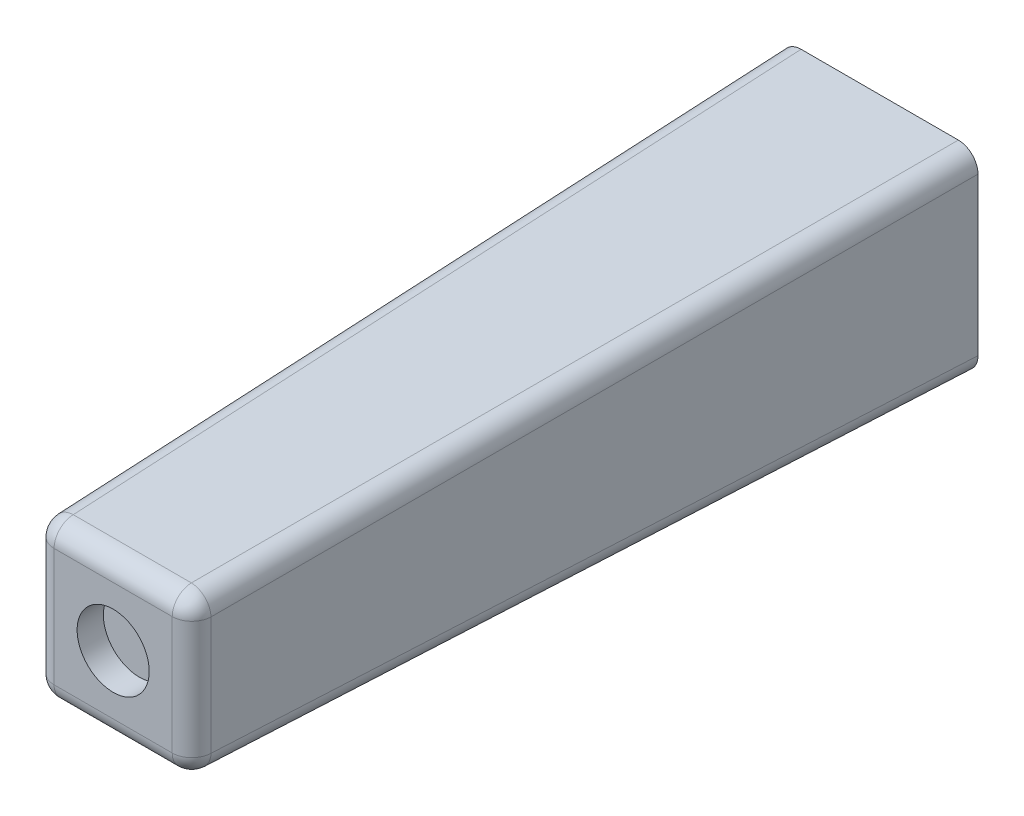
SolidWorks part; units mm, degrees
ref_plane "Спереди" through (0, 0, 0) normal (0, 0, 1) x (1, 0, 0)
ref_plane "Сверху" through (0, 0, 0) normal (0, 1, 0) x (1, 0, 0)
ref_plane "Справа" through (0, 0, 0) normal (1, 0, 0) x (0, 0, -1)
other "Configuration Table"
sketch "Sketch1" plane through (0, 0, 0) normal (0, 0, 1) x (1, 0, 0)
  line L1 (-7.5, -7.5) -> (7.5, -7.5)
  line L2 (-7.5, -7.5) -> (-7.5, 7.5)
  line L3 (-7.5, 7.5) -> (7.5, 7.5)
  line L4 (7.5, -7.5) -> (7.5, 7.5)
  line L5 (-7.5, -7.5) -> (7.5, 7.5) construction
  line L6 (-7.5, 7.5) -> (7.5, -7.5) construction
  point P0 (0, 0)
  dimension "D1" = 15
  dimension "D2" = 15
extrude "Boss-Extrude1" add sketch "Sketch1" along normal blind 58.5 draft 1.5
sketch "Sketch2" plane through (0, 0, 0) normal (0, 0, -1) x (-1, 0, 0)
  circle A0 centre (0, 0) radius 1.5
  dimension "D1" = 3
extrude "Cut-Extrude1" cut sketch "Sketch2" against normal blind 10
sketch "Sketch3" plane through (0, 0, 58.5) normal (0, 0, 1) x (1, 0, 0)
  circle A0 centre (0, 0) radius 2.75
  dimension "D1" = 5.5
extrude "Cut-Extrude2" cut sketch "Sketch3" against normal blind 2
fillet "Fillet1" radius 1.5 8 edges at (0, 5.9681, 58.5) (5.9681, 0, 58.5) (0, -5.9681, 58.5) (-5.9681, 0, 58.5) (-6.7341, -6.7341, 29.25) (6.7341, 6.7341, 29.25) (-6.7341, 6.7341, 29.25) (6.7341, -6.7341, 29.25)
fillet "Fillet2" radius 0.5 1 edges at (-1.5, 0, 0)
